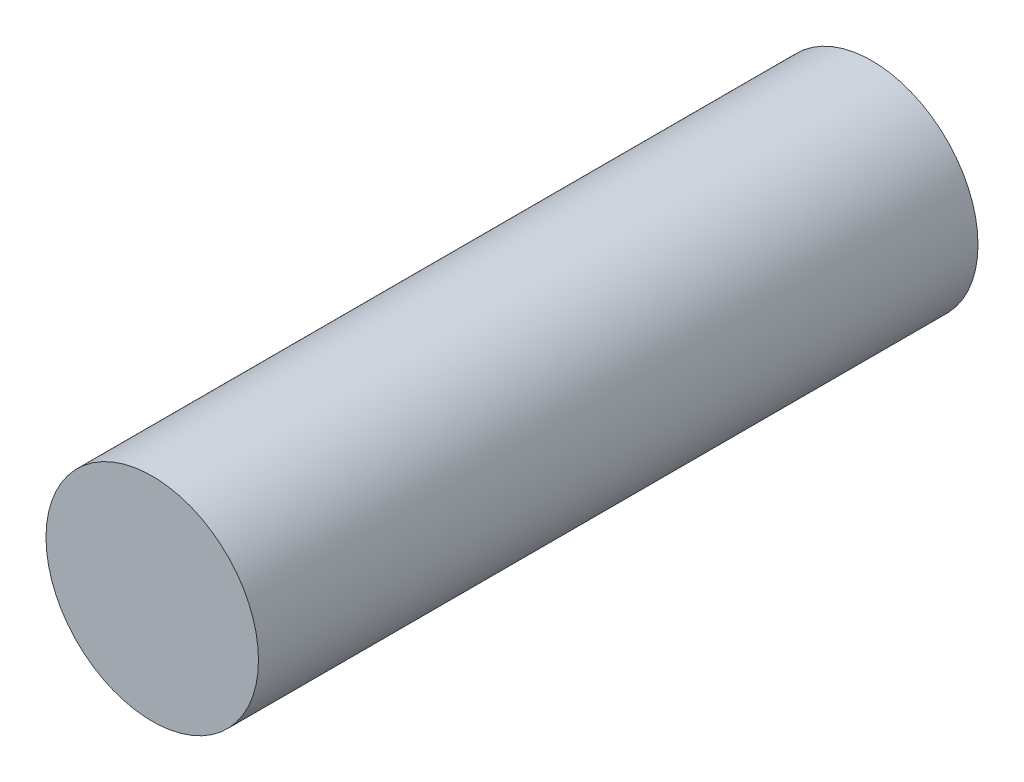
SolidWorks part; units mm, degrees
ref_plane "前视基准面" through (0, 0, 0) normal (0, 0, 1) x (1, 0, 0)
ref_plane "上视基准面" through (0, 0, 0) normal (0, 1, 0) x (1, 0, 0)
ref_plane "右视基准面" through (0, 0, 0) normal (1, 0, 0) x (0, 0, -1)
sketch "草图1" plane through (0, 0, 0) normal (0, 0, 1) x (1, 0, 0)
  circle A0 centre (0, 0) radius 22.1471
extrude "凸台-拉伸1" add sketch "草图1" along normal blind 150
sketch "草图2" plane through (0, 0, 150) normal (0, 0, 1) x (1, 0, 0)
  line L0 (-0.3304, -0.0738) -> (-5.3304, -0.0738)
  line L1 (-0.3304, -0.0738) -> (-0.3304, -5.0738)
  line L2 (-0.3304, -0.0738) -> (-0.3304, 4.9262)
  line L3 (-0.3304, -0.0738) -> (4.6696, -0.0738)
  point P4 (0, 0)
  point P8 (0, 0)
  point P9 (0, 0)
  point P10 (0, 0)
  point P11 (0, 0)
  point P12 (0, 0)
  point P13 (0, 0)
sketch "草图3" plane through (0, 0, 0) normal (0, 0, -1) x (-1, 0, 0)
  line L0 (0, 0) -> (5, 0)
  line L1 (5, 0) -> (-5, 0)
